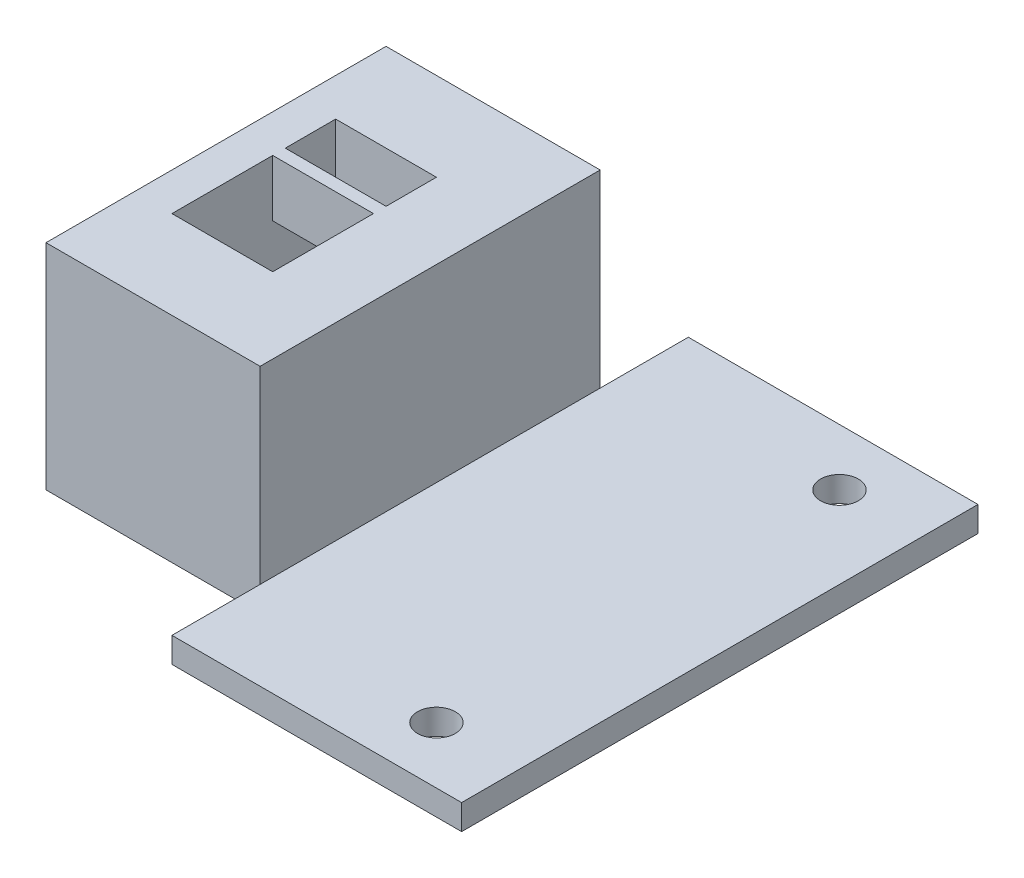
SolidWorks part; units mm, degrees
ref_plane "Alzado" through (0, 0, 0) normal (0, 0, 1) x (1, 0, 0)
ref_plane "Planta" through (0, 0, 0) normal (0, 1, 0) x (1, 0, 0)
ref_plane "Vista lateral" through (0, 0, 0) normal (1, 0, 0) x (0, 0, -1)
sketch "Croquis1" plane through (0, 0, 0) normal (0, 0, 1) x (1, 0, 0)
  line L0 (-65.3731, 23.1868) -> (-48.3731, 23.1868)
  line L1 (-25.3731, 6.1868) -> (-65.3731, 6.1868)
  line L2 (-65.3731, 23.1868) -> (-65.3731, 6.1868)
  line L5 (-48.3731, 23.1868) -> (-48.3731, 8.1868)
  line L6 (-48.3731, 8.1868) -> (-25.3731, 8.1868)
  line L7 (-25.3731, 8.1868) -> (-25.3731, 6.1868)
  dimension "D1" = 17
extrude "Saliente-Extruir1" add sketch "Croquis1" along normal blind 41
sketch "Croquis2" plane through (0, 6.1868, 0) normal (0, -1, 0) x (1, 0, 0)
  line L0 (-25.3731, 41) -> (-25.3731, 0) construction
  line L1 (-65.3731, 41) -> (-25.3731, 41) construction
  circle A0 centre (-31.8731, 36.5) radius 1.5
  circle A1 centre (-31.8731, 4.5) radius 1.5
  dimension "D1" = 6.5
  dimension "D2" = 32
  dimension "D3" = 4.5
extrude "Cortar-Extruir1" cut sketch "Croquis2" against normal up to vertex (2 mm away)
sketch "Croquis3" plane through (0, 6.1868, 0) normal (0, -1, 0) x (1, 0, 0)
  line L2 (-62.3731, 27) -> (-62.3731, 14)
  line L4 (-54.3731, 27) -> (-54.3731, 14)
  line L7 (-65.3731, 41) -> (-48.3731, 41)
  line L8 (-65.3731, 41) -> (-65.3731, 34)
  line L9 (-65.3731, 34) -> (-48.3731, 34)
  line L10 (-48.3731, 41) -> (-48.3731, 34)
  line L11 (-65.3731, 0) -> (-48.3731, 0)
  line L12 (-65.3731, 0) -> (-65.3731, 7)
  line L13 (-65.3731, 7) -> (-48.3731, 7)
  line L14 (-48.3731, 0) -> (-48.3731, 7)
  line L15 (-62.3731, 27) -> (-54.3731, 27)
  line L19 (-62.3731, 14) -> (-54.3731, 14)
  dimension "D2" = 8
  dimension "D3" = 13
  dimension "D5" = 17
extrude "Cortar-Extruir2" cut sketch "Croquis3" against normal up to vertex
sketch "Croquis4" plane through (0, 23.1868, 0) normal (0, 1, 0) x (1, 0, 0)
  line L0 (-54.3731, -14) -> (-54.3731, -27) construction
  line L1 (-54.3731, -19) -> (-62.3731, -19)
  line L2 (-54.3731, -19) -> (-54.3731, -18)
  line L3 (-54.3731, -18) -> (-62.3731, -18)
  line L4 (-62.3731, -19) -> (-62.3731, -18)
  line L5 (-62.3731, -27) -> (-62.3731, -14) construction
  line L6 (-62.3731, -14) -> (-54.3731, -14) construction
  dimension "D1" = 4
  dimension "D2" = 1
extrude "Saliente-Extruir2" add sketch "Croquis4" against normal blind 4.5
